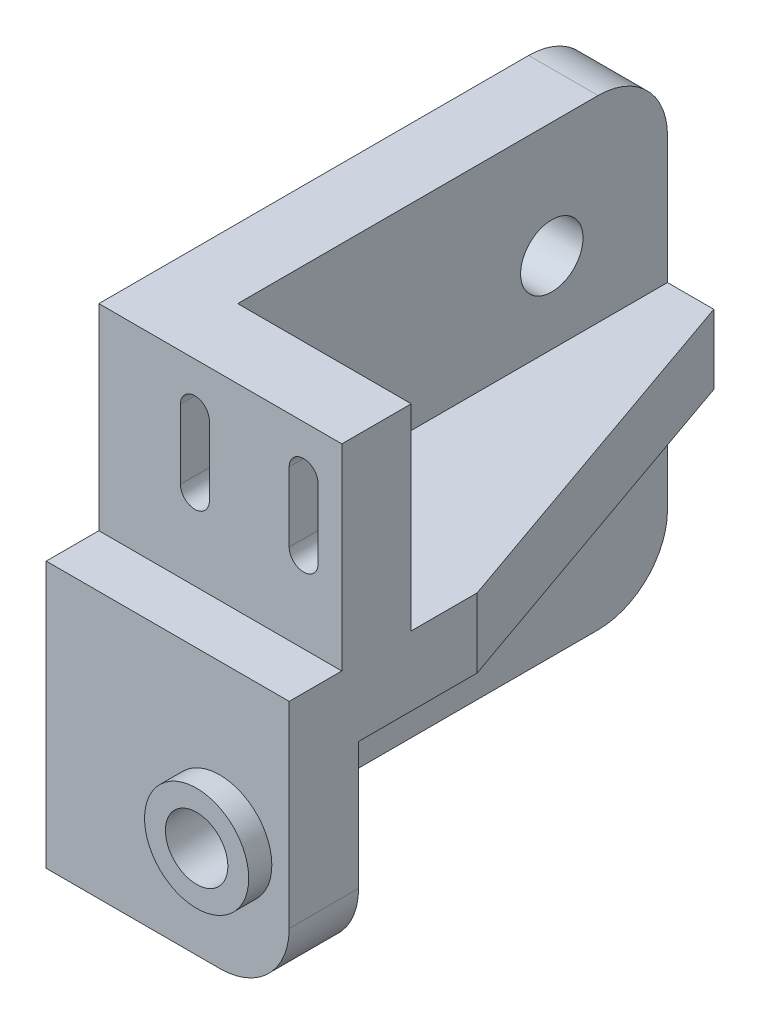
SolidWorks part; units mm, degrees
ref_plane "Front Plane" through (0, 0, 0) normal (0, 0, 1) x (1, 0, 0)
ref_plane "Top Plane" through (0, 0, 0) normal (0, 1, 0) x (1, 0, 0)
ref_plane "Right Plane" through (0, 0, 0) normal (1, 0, 0) x (0, 0, -1)
sketch "Sketch1" plane through (0, 0, 0) normal (1, 0, 0) x (0, 0, -1)
  line L1 (0, 0) -> (43.15, 0)
  line L2 (0, 0) -> (0, 40)
  line L3 (0, 40) -> (43.15, 40)
  line L4 (43.15, 0) -> (43.15, 40)
  dimension "D1" = 43.15
  dimension "D2" = 40
extrude "Boss-Extrude1" add sketch "Sketch1" along normal blind 6 contours L3 L4 L1 L2
sketch "Sketch2" plane through (0, 0, 0) normal (1, 0, 0) x (0, 0, -1)
  line L0 (0, 0) -> (0, 40) construction
  line L1 (-4.55, 23) -> (0, 23)
  line L2 (-4.55, 23) -> (-4.55, 0)
  line L3 (-4.55, 0) -> (1.45, 0)
  line L4 (1.45, 17) -> (1.45, 0)
  line L5 (0, 0) -> (43.15, 0) construction
  line L6 (1.45, 23) -> (6, 23) construction
  line L7 (0, 40) -> (6, 40)
  line L8 (0, 40) -> (0, 23)
  line L9 (0, 23) -> (1.45, 23) construction
  line L10 (6, 40) -> (6, 23)
  line L11 (6, 23) -> (43.15, 23)
  line L12 (1.45, 23) -> (1.45, 17) construction
  line L13 (1.45, 17) -> (43.15, 17)
  line L14 (43.15, 23) -> (43.15, 17)
  line L15 (1.45, 23) -> (6, 23) construction
  line L16 (1.45, 23) -> (1.45, 17) construction
  line L17 (0, 23) -> (1.45, 23) construction
  line L18 (43.15, 0) -> (43.15, 40) construction
  dimension "D1" = 4.55
  dimension "D3" = 23
  dimension "D4" = 6
  dimension "D2" = 6
  dimension "D6" = 6
extrude "Boss-Extrude2" add sketch "Sketch2" along normal blind 21
chamfer "Chamfer1" distance 11 distance2 31.45 1 edges at (21, 20, -43.15)
hole_wizard "Ø5.4mm Dowel Hole1" positions "Sketch6" profile "Sketch7" hole size "Ø5.0" standard "ANSI Metric" end condition through all
sketch "Sketch6" plane through (0, 0, 0) normal (-1, 0, 0) x (0, 0, 1)
  line L0 (0, 40) -> (-43.15, 40) construction
  line L1 (-43.15, 0) -> (-43.15, 40) construction
  line L2 (4.55, 0) -> (-43.15, 0) construction
  point P0 (-33.15, 30)
  point P2 (-33.15, 10)
  dimension "D1" = 10
  dimension "D2" = 10
  dimension "D3" = 10
sketch "Sketch7" plane through (0, 30, -33.15) normal (0, 1, 0) x (0, 0, 1)
  line L0 (0, 0) -> (0, 21)
  line L1 (0, 21) -> (2.7, 21)
  line L2 (2.7, 21) -> (2.7, 0)
  line L5 (2.7, 0) -> (0, 0)
  line L11 (0, -6.35) -> (0, 107.95) construction
  dimension "Thru Hole Dia." = 5.4
  dimension "Thru Hole Depth" = 21
sketch "Sketch8" plane through (0, 0, 4.55) normal (0, 0, 1) x (1, 0, 0)
  line L0 (21, 0) -> (0, 0) construction
  line L1 (21, 23) -> (21, 0) construction
  circle A0 centre (15, 10) radius 4.5
  dimension "D3" = 9
  dimension "D1" = 10
  dimension "D2" = 6
extrude "Boss-Extrude3" add sketch "Sketch8" along normal blind 2
hole_wizard "Ø5.4mm Dowel Hole2" positions "Sketch9" profile "Sketch10" hole size "Ø5.0" standard "ANSI Metric" end condition through all
sketch "Sketch9" plane through (0, 0, 6.55) normal (0, 0, 1) x (1, 0, 0)
  point P0 (15, 10)
sketch "Sketch10" plane through (15, 10, 6.55) normal (1, 0, 0) x (0, -1, 0)
  line L0 (0, 0) -> (0, 49.7)
  line L1 (0, 49.7) -> (2.7, 49.7)
  line L2 (2.7, 49.7) -> (2.7, 0)
  line L5 (2.7, 0) -> (0, 0)
  line L11 (0, -6.35) -> (0, 107.95) construction
  dimension "Thru Hole Dia." = 5.4
  dimension "Thru Hole Depth" = 49.7
sketch "Sketch11" plane through (0, 0, 0) normal (0, 0, 1) x (1, 0, 0)
  line L0 (17.7, 36) -> (17.7, 30) construction
  line L1 (18.95, 36) -> (18.95, 30)
  line L2 (16.45, 36) -> (16.45, 30)
  line L3 (21, 40) -> (21, 23) construction
  line L4 (21, 40) -> (0, 40) construction
  line L5 (8.3, 36) -> (8.3, 30) construction
  line L6 (9.55, 36) -> (9.55, 30)
  line L7 (7.05, 36) -> (7.05, 30)
  arc A0 (18.95, 36) -> (16.45, 36) centre (17.7, 36) ccw
  arc A1 (16.45, 30) -> (18.95, 30) centre (17.7, 30) ccw
  arc A2 (9.55, 36) -> (7.05, 36) centre (8.3, 36) ccw
  arc A3 (7.05, 30) -> (9.55, 30) centre (8.3, 30) ccw
  point P2 (17.7, 33)
  point P14 (8.3, 33)
  dimension "D2" = 1.25
  dimension "D1" = 6
  dimension "D3" = 2.05
  dimension "D4" = 4
  dimension "D5" = 2
extrude "Cut-Extrude1" cut sketch "Sketch11" against normal through all
fillet "Fillet1" radius 6 1 edges at (21, 0, 1.55)
fillet "Fillet2" radius 6 2 edges at (3, 40, -43.15) (3, 0, -43.15)
equation "\"D4@Sketch2\"=\"D2@Sketch2\""
equation "\"D6@Sketch2\"=\"D2@Sketch2\""
equation "\"D3@Sketch6\"=\"D1@Sketch6\""
equation "\"D2@Sketch6\"=\"D1@Sketch6\""
